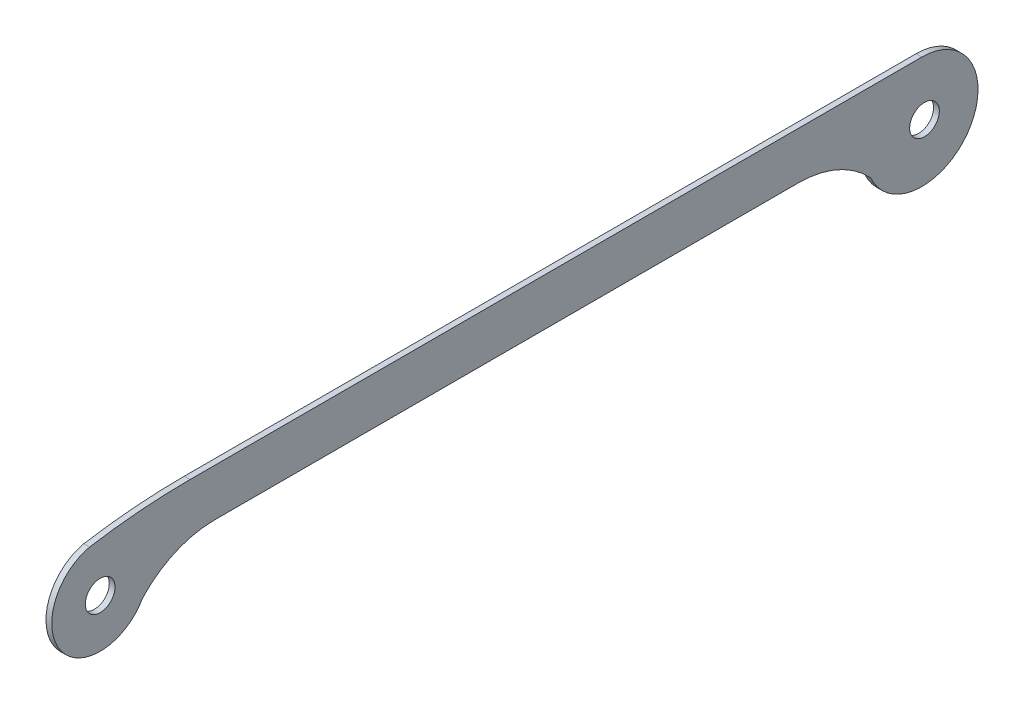
SolidWorks part; units mm, degrees
ref_plane "前基準面" through (0, 0, 0) normal (0, 0, 1) x (1, 0, 0)
ref_plane "上基準面" through (0, 0, 0) normal (0, 1, 0) x (1, 0, 0)
ref_plane "右基準面" through (0, 0, 0) normal (1, 0, 0) x (0, 0, -1)
sketch "草圖1" plane through (0, 0, 0) normal (1, 0, 0) x (0, 0, -1)
  line L0 (251.5013, 74.383) -> (100.2019, 74.383)
  line L1 (249.0955, 86.633) -> (93.7643, 86.633)
  line L2 (249.0955, 86.633) -> (283.5525, 86.633)
  line L3 (175.8516, 72.2487) -> (175.8516, 48.8429) construction
  line L4 (270.2438, 66.1603) -> (270.2642, 66.1381)
  arc A0 (67.7178, 84.4987) -> (81.4594, 66.1603) centre (70.4772, 72.2487) ccw
  circle A1 centre (70.4772, 72.2487) radius 3.85
  arc A2 (93.7643, 86.633) -> (67.7178, 84.4987) centre (93.7643, -73.3691) ccw
  circle A4 centre (284.2272, 72.2487) radius 3.85
  arc A5 (283.5525, 86.633) -> (270.2642, 66.1381) centre (283.5525, 72.0777) cw
  arc A6 (100.2019, 74.383) -> (81.4594, 66.1603) centre (100.2019, 48.9111) ccw
  arc A7 (251.5013, 74.383) -> (270.2438, 66.1603) centre (251.5013, 48.9111) cw
  point P8 (171.4299, 74.383)
  point P16 (171.4299, 86.633)
  dimension "D1" = 213.75
  dimension "D2" = 14.5553
extrude "填料-伸長1" add sketch "草圖1" along normal blind 1.5
